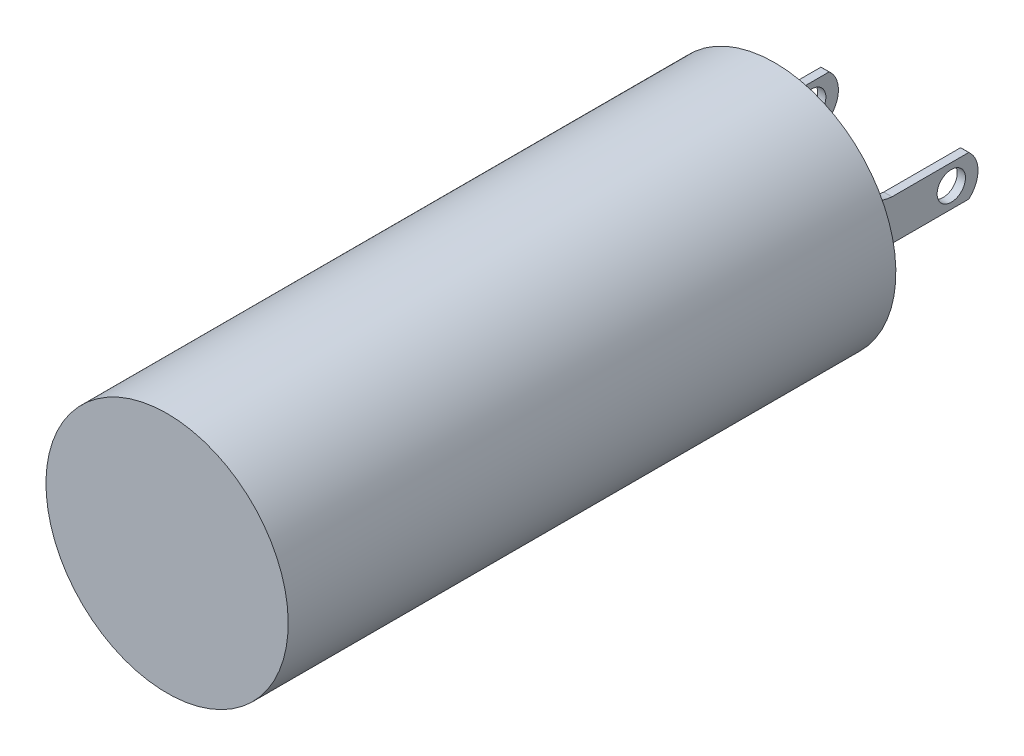
SolidWorks part; units mm, degrees
material "minimotor"
ref_plane "Front Plane" through (0, 0, 0) normal (0, 0, 1) x (1, 0, 0)
ref_plane "Top Plane" through (0, 0, 0) normal (0, 1, 0) x (1, 0, 0)
ref_plane "Right Plane" through (0, 0, 0) normal (1, 0, 0) x (0, 0, -1)
sketch "Sketch1" plane through (0, 0, 0) normal (1, 0, 0) x (0, 0, -1)
  line L0 (0, 0) -> (0, 2.9972)
  line L1 (0, 2.9972) -> (15.0368, 2.9972)
  line L2 (15.4178, 0) -> (15.4178, 1.5875)
  line L3 (15.4178, 0) -> (0, 0)
  line L4 (15.4178, 1.5875) -> (15.0368, 1.5875)
  line L5 (15.0368, 1.5875) -> (15.0368, 2.9972)
  dimension "D1" = 15.0368
  dimension "D2" = 2.9972
  dimension "D3" = 0.381
  dimension "D4" = 1.5875
revolve "Revolve1" add sketch "Sketch1" angle 360 about L3
ref_plane "Plane1" through (1.6256, 0, 0) normal (1, 0, 0) x (0, 0, -1)
sketch "Sketch3" plane through (1.6256, 0, 0) normal (1, 0, 0) x (0, 0, -1)
  line L0 (15.0368, 0.635) -> (15.0368, -0.635)
  line L1 (15.0368, -0.635) -> (15.6718, -0.635)
  line L2 (15.0368, -2.9972) -> (15.0368, 2.9972) construction
  line L3 (0, 0) -> (15.0368, 0) construction
  line L4 (15.0368, 0.635) -> (15.6718, 0.635)
  line L5 (16.1087, 0.5004) -> (18.0086, 0.5004)
  line L6 (16.1087, -0.5004) -> (18.0086, -0.5004)
  arc A0 (15.6718, 0.635) -> (16.1087, 0.5004) centre (16.1928, 1.5494) ccw
  arc A1 (15.6718, -0.635) -> (16.1087, -0.5004) centre (16.1928, -1.5494) cw
  arc A2 (18.0086, 0.5004) -> (18.0086, -0.5004) centre (17.5768, 0) cw
  circle A3 centre (17.5768, 0) radius 0.3505
  dimension "D5" = 0.701
  dimension "D1" = 0.635
  dimension "D2" = 1.27
  dimension "D3" = 1.0008
  dimension "D4" = 2.9718
  dimension "D6" = 2.54
extrude "Boss-Extrude1" add sketch "Sketch3" along normal blind 0.2032
mirror "Mirror1" about plane through (0, 0, 0) normal (1, 0, 0) of "Boss-Extrude1"
